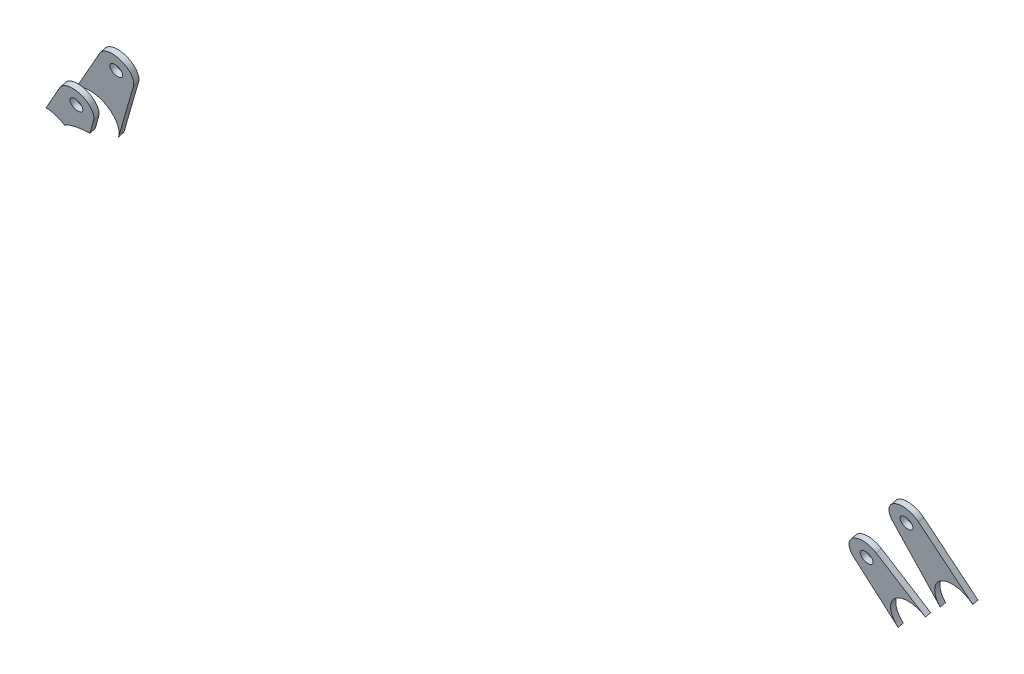
SolidWorks part; units mm, degrees
material "1.0545 (S355N)"
ref_plane "Płaszczyzna XY" through (0, 0, 0) normal (0, 0, 1) x (1, 0, 0)
ref_plane "Płaszczyzna XZ" through (0, 0, 0) normal (0, 1, 0) x (1, 0, 0)
ref_plane "Płaszczyzna YZ" through (0, 0, 0) normal (1, 0, 0) x (0, 0, -1)
ref_plane "Płaszczyzna2" through (0.7348, -51.5158, 211.8917) normal (-0.0034, 0.2362, -0.9717) x (-1, -0.0008, 0.0033)
sketch "Szkic1" plane through (0.7348, -51.5158, 211.8917) normal (-0.0034, 0.2362, -0.9717) x (-1, -0.0008, 0.0033)
  line L0 (-209.4413, 282.0357) -> (-187.1693, 315.893)
  line L1 (-170.579, 306.7521) -> (-188.0631, 268.1548)
  line L2 (268.7305, 315.855) -> (290.9421, 281.7503)
  line L3 (252.0992, 306.7886) -> (269.495, 267.9329)
  circle A4 centre (-179.2326, 310.6721) radius 3.5
  circle A5 centre (260.7699, 310.6705) radius 3.5
  arc A6 (-170.579, 306.7521) -> (-187.1693, 315.893) centre (-179.2326, 310.6721) ccw
  arc A7 (268.7305, 315.855) -> (252.0992, 306.7886) centre (260.7699, 310.6705) ccw
  circle A8 centre (-179.2326, 310.6721) radius 9.5 construction
  circle A9 centre (260.7699, 310.6705) radius 9.5 construction
  spline S1 degree 3 poles (-199.1687, 287.7293) (-174.1695, 287.5315) (-174.3845, 260.3594) (-199.3837, 260.5572) (-224.3829, 260.755) (-224.1679, 287.9271) (-199.1687, 287.7293) (-174.1695, 287.5315) (-174.3845, 260.3594) knots -0.5 0 0 0 0.5 0.5 0.5 1 1 1 1.5 1.5 1.5 weights 1 0.333333 0.333333 1 0.333333 0.333333 1 0.333333 0.333333 only from (-199.1687, 287.7293) to (-199.1687, 287.7293)
  spline S3 degree 3 poles (269.495, 267.9329) (264.2736, 279.5956) (272.1002, 287.5459) (280.8438, 287.4768) (284.4893, 287.4479) (288.3341, 285.7547) (290.9421, 281.7503) knots 0.191303 0.191303 0.191303 0.191303 0.5 0.5 0.5 0.669346 0.669346 0.669346 0.669346 weights 0.527563 0.430925 0.588404 1 0.774206 0.624886 0.552041
  dimension "D2" = 6
  dimension "D1" = 7
extrude "Dodanie-wyciągnięcie1" add sketch "Szkic1" along normal blind 3 contours L0 S1 L1 A6 A4 | L3 S3 L2 A7 A5
ref_plane "Płaszczyzna3" through (0.8123, -56.9493, 234.2406) normal (-0.0034, 0.2362, -0.9717) x (-1, -0.0008, 0.0033)
sketch "Szkic2" plane through (0.8123, -56.9493, 234.2406) normal (-0.0034, 0.2362, -0.9717) x (-1, -0.0008, 0.0033)
  line L2 (-171.0975, 305.7658) -> (-188.7472, 276.5008)
  line L3 (-186.205, 317.1246) -> (-208.0058, 293.5675)
  line L5 (280.8328, 297.2725) -> (268.7305, 315.855)
  line L6 (256.4127, 297.1539) -> (252.0992, 306.7886)
  line L7 (252.0992, 306.7886) -> (269.495, 267.9329) construction
  line L9 (268.7305, 315.855) -> (290.9421, 281.7503) construction
  circle A0 centre (-179.2326, 310.6721) radius 3.5 construction
  arc A1 (268.7305, 315.855) -> (252.0992, 306.7886) centre (260.7699, 310.6705) ccw
  circle A2 centre (260.7699, 310.6705) radius 9.5 construction
  circle A3 centre (260.7699, 310.6705) radius 3.5 construction
  circle A4 centre (-179.2326, 310.6721) radius 3.5
  arc A6 (-171.0975, 305.7658) -> (-186.205, 317.1246) centre (-179.2326, 310.6721) ccw
  circle A7 centre (260.7699, 310.6705) radius 3.5
  circle A8 centre (-179.2326, 310.6721) radius 9.5 construction
  spline S2 degree 3 poles (292.1676, 278.0187) (286.0519, 263.5777) (271.5279, 265.3645) (268.572, 280.9214) knots 0 0 0 0 1 1 1 1 weights 1 0.541532 0.541532 1
  spline S3 degree 3 poles (271.5448, 292.7883) (276.2011, 298.3885) (283.1172, 299.0264) (288.5629, 294.358) knots 0 0 0 0 1 1 1 1 weights 1 0.820223 0.820223 1
  spline S5 degree 3 poles (336.0645, 277.7054) (330.3085, 253.377) (279.3909, 265.424) (285.1469, 289.7523) (290.903, 314.0807) (341.8205, 302.0337) (336.0645, 277.7054) (330.3085, 253.377) (279.3909, 265.424) knots -0.5 0 0 0 0.5 0.5 0.5 1 1 1 1.5 1.5 1.5 weights 1 0.333333 0.333333 1 0.333333 0.333333 1 0.333333 0.333333 only from (336.0645, 277.7054) to (336.0645, 277.7054)
  spline S7 degree 3 poles (268.572, 280.9214) (245.5287, 263.2245) (205.3718, 262.6049) (209.7329, 280.0135) (214.0939, 297.4221) (256.2797, 306.1407) (271.5448, 292.7883) knots 0 0 0 0 0.5 0.5 0.5 1 1 1 1 weights 1 0.488411 0.488411 1 0.488411 0.488411 1
  spline S9 degree 3 poles (-199.0912, 297.5247) (-174.092, 297.3269) (-174.307, 270.1548) (-199.3062, 270.3526) (-224.3054, 270.5504) (-224.0904, 297.7225) (-199.0912, 297.5247) (-174.092, 297.3269) (-174.307, 270.1548) knots -0.5 0 0 0 0.5 0.5 0.5 1 1 1 1.5 1.5 1.5 weights 1 0.333333 0.333333 1 0.333333 0.333333 1 0.333333 0.333333 only from (-199.0912, 297.5247) to (-199.0912, 297.5247)
  dimension "D2" = 6
  dimension "D1" = 6
extrude "Dodanie-wyciągnięcie2" add sketch "Szkic2" along normal blind 3 separate body
